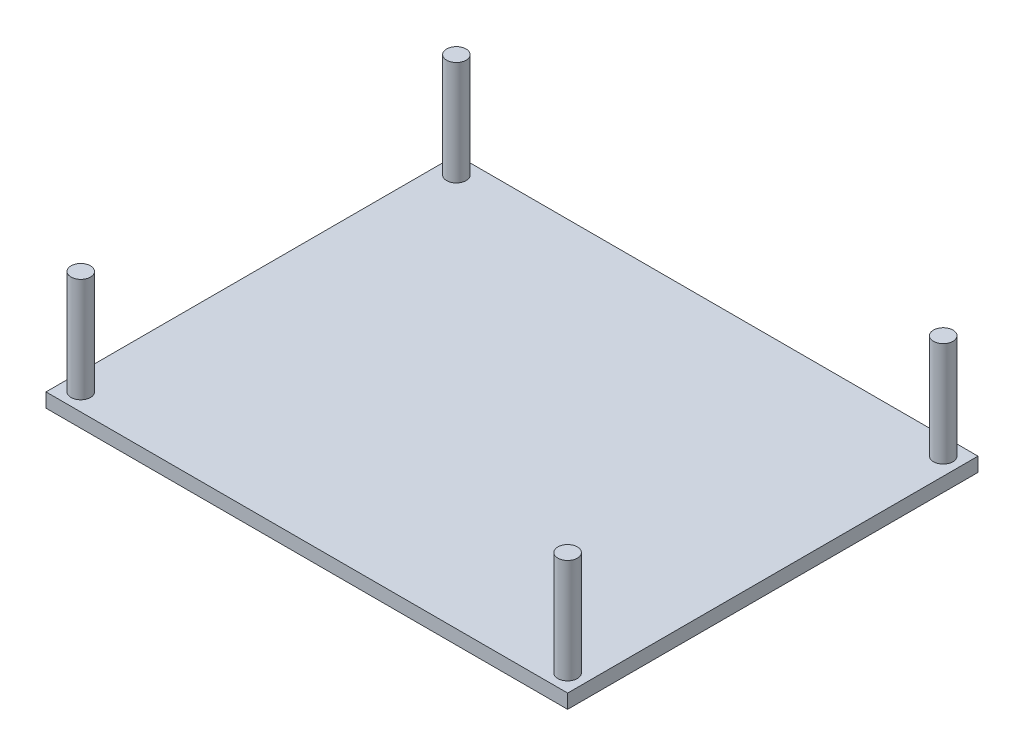
SolidWorks part; units mm, degrees
ref_plane "Front Plane" through (0, 0, 0) normal (0, 0, 1) x (1, 0, 0)
ref_plane "Top Plane" through (0, 0, 0) normal (0, 1, 0) x (1, 0, 0)
ref_plane "Right Plane" through (0, 0, 0) normal (1, 0, 0) x (0, 0, -1)
sketch "Sketch1" plane through (0, 0, 0) normal (0, 1, 0) x (1, 0, 0)
  line L1 (0, 0) -> (75, 0)
  line L2 (0, 0) -> (0, 59)
  line L3 (0, 59) -> (75, 59)
  line L4 (75, 0) -> (75, 59)
  dimension "D1" = 59
  dimension "D2" = 75
extrude "Boss-Extrude1" add sketch "Sketch1" against normal blind 2.032
sketch "Sketch2" plane through (0, 0, 0) normal (0, 1, 0) x (1, 0, 0)
  line L0 (-15.9599, 29.5) -> (88.6505, 29.5) construction
  line L1 (75, 59) -> (0, 59) construction
  line L4 (0, 0) -> (75, 0) construction
  line L5 (0, 59) -> (0, 0) construction
  line L6 (75, 0) -> (75, 59) construction
  circle A0 centre (2.5, 2.5) radius 1.4
  circle A1 centre (72.5, 2.5) radius 1.4
  circle A2 centre (72.5, 56.5) radius 1.4
  circle A3 centre (2.5, 56.5) radius 1.4
  dimension "D2" = 2.8
  dimension "D3" = 2.5
  dimension "D4" = 2.5
  dimension "D5" = 2.8
  dimension "D6" = 2.5
  dimension "D7" = 2.5
  dimension "D1" = 29.5
extrude "Boss-Extrude2" add sketch "Sketch2" along normal blind 15
